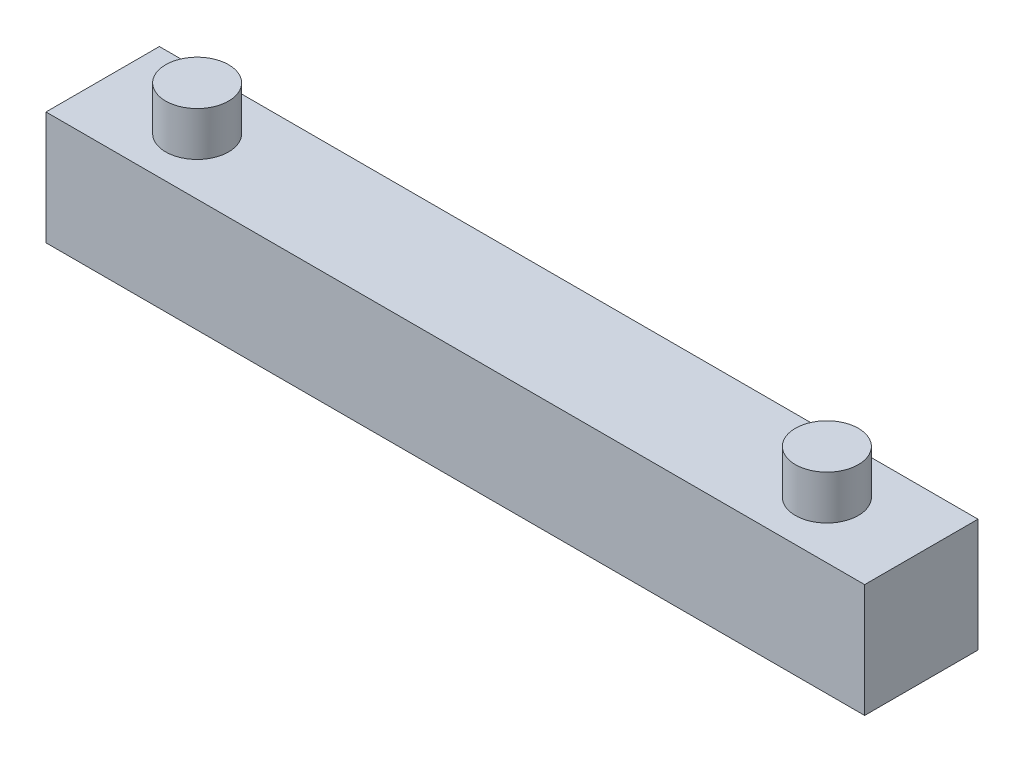
SolidWorks part; units mm, degrees
ref_plane "Front Plane" through (0, 0, 0) normal (0, 0, 1) x (1, 0, 0)
ref_plane "Top Plane" through (0, 0, 0) normal (0, 1, 0) x (1, 0, 0)
ref_plane "Right Plane" through (0, 0, 0) normal (1, 0, 0) x (0, 0, -1)
sketch "Sketch1" plane through (0, 0, 0) normal (0, 1, 0) x (1, 0, 0)
  line L1 (0, 0) -> (65, 0)
  line L2 (0, 0) -> (0, 9)
  line L3 (0, 9) -> (65, 9)
  line L4 (65, 0) -> (65, 9)
  dimension "D1" = 65
  dimension "D2" = 9
extrude "Boss-Extrude1" add sketch "Sketch1" along normal blind 9
sketch "Sketch2" plane through (0, 9, 0) normal (0, 1, 0) x (1, 0, 0)
  line L0 (32.5, 22.9123) -> (32.5, -15.2336) construction
  line L1 (0, 9) -> (0, 0) construction
  line L2 (65, 9) -> (0, 9) construction
  circle A0 centre (7.5, 4.5) radius 2.5
  circle A1 centre (57.5, 4.5) radius 2.5
  dimension "D1" = 2.5
  dimension "D2" = 32.5
  dimension "D3" = 4.5
  dimension "D4" = 50
extrude "Boss-Extrude2" add sketch "Sketch2" along normal blind 3.5
